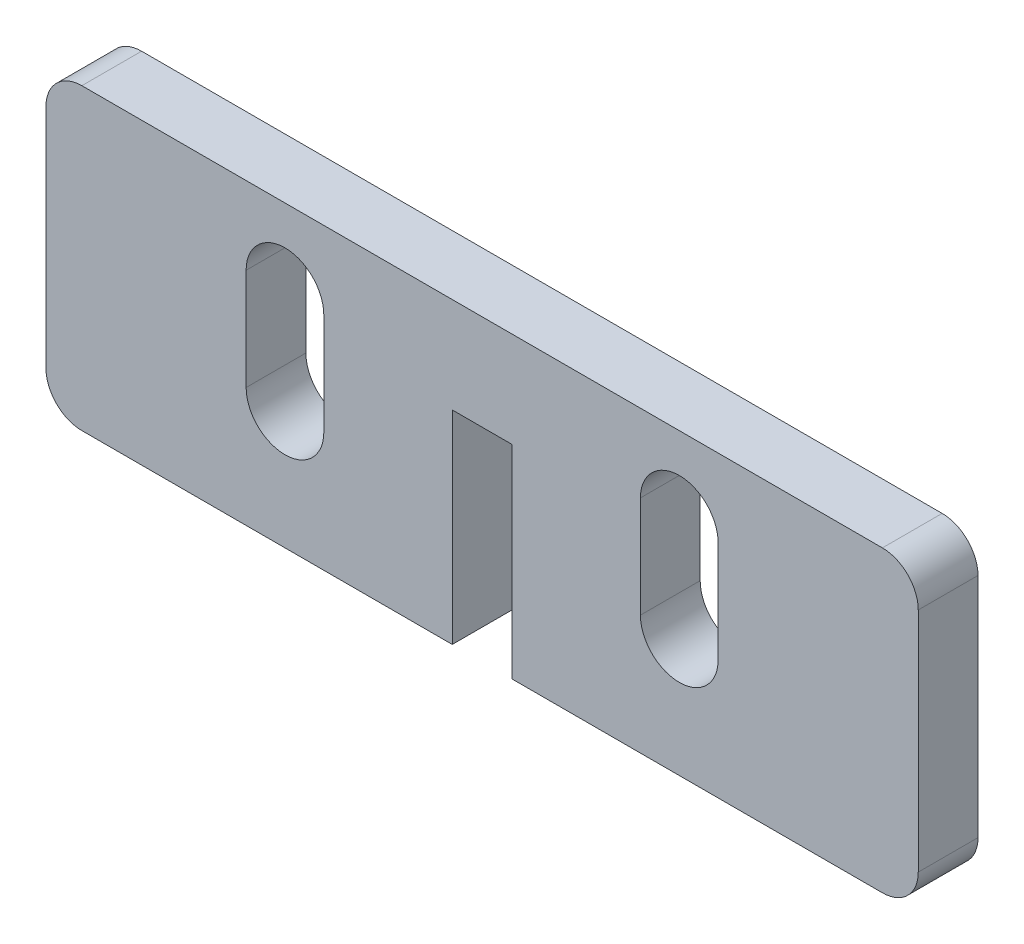
SolidWorks part; units mm, degrees
ref_plane "前视基准面" through (0, 0, 0) normal (0, 0, 1) x (1, 0, 0)
ref_plane "上视基准面" through (0, 0, 0) normal (0, 1, 0) x (1, 0, 0)
ref_plane "右视基准面" through (0, 0, 0) normal (1, 0, 0) x (0, 0, -1)
sketch "草图1" plane through (0, 0, 0) normal (0, 0, 1) x (1, 0, 0)
  line L0 (-16.5, -2.5) -> (-16.5, 6) construction
  line L1 (33.5, -12.5) -> (-33.5, -12.5) construction
  line L2 (36.5, -9.5) -> (36.5, 9.5)
  line L3 (33.5, 12.5) -> (-33.5, 12.5)
  line L4 (-36.5, -9.5) -> (-36.5, 9.5)
  line L5 (0, 12.5) -> (0, -12.5) construction
  line L6 (36.5, 0) -> (-36.5, 0) construction
  line L7 (2.5, 2.5) -> (-2.5, 2.5)
  line L8 (2.5, 2.5) -> (2.5, -12.5)
  line L9 (2.5, -12.5) -> (-2.5, -12.5) construction
  line L10 (-2.5, 2.5) -> (-2.5, -12.5)
  line L11 (0, -12.5) -> (0, 2.5) construction
  line L12 (2.5, -5) -> (-2.5, -5) construction
  line L13 (-19.75, -2.5) -> (-19.75, 6)
  line L14 (-13.25, -2.5) -> (-13.25, 6)
  line L15 (16.5, -2.5) -> (16.5, 6) construction
  line L16 (19.75, -2.5) -> (19.75, 6)
  line L17 (13.25, -2.5) -> (13.25, 6)
  line L18 (-33.5, -12.5) -> (-2.5, -12.5)
  line L19 (2.5, -12.5) -> (33.5, -12.5)
  arc A0 (-19.75, -2.5) -> (-13.25, -2.5) centre (-16.5, -2.5) ccw
  arc A1 (-13.25, 6) -> (-19.75, 6) centre (-16.5, 6) ccw
  arc A2 (19.75, -2.5) -> (13.25, -2.5) centre (16.5, -2.5) cw
  arc A3 (13.25, 6) -> (19.75, 6) centre (16.5, 6) cw
  arc A4 (33.5, -12.5) -> (36.5, -9.5) centre (33.5, -9.5) ccw
  arc A5 (-33.5, -12.5) -> (-36.5, -9.5) centre (-33.5, -9.5) cw
  arc A6 (36.5, 9.5) -> (33.5, 12.5) centre (33.5, 9.5) ccw
  arc A7 (-33.5, 12.5) -> (-36.5, 9.5) centre (-33.5, 9.5) ccw
  point P0 (0, 0)
  point P4 (0, -5)
  point P13 (-16.5, 1.75)
  point P21 (-16.5, 9.25)
  point P22 (-16.5, -5.75)
  point P25 (16.5, 1.75)
  point P32 (36.5, -12.5)
  point P37 (36.5, 12.5)
  point P40 (-36.5, 12.5)
  dimension "D9" = 3
  dimension "D1" = 73
  dimension "D2" = 25
  dimension "D3" = 5
  dimension "D4" = 15
  dimension "D5" = 3.25
  dimension "D6" = 10.75
  dimension "D7" = 6.5
  dimension "D8" = 15
extrude "凸台-拉伸1" add sketch "草图1" along normal blind 5
sketch "草图3" plane through (0, 0, 0) normal (0, 0, -1) x (-1, 0, 0)
  line L0 (-2.5, 2.5) -> (-2.5, 4.5)
  line L1 (-2.5, 4.5) -> (2.5, 4.5)
  line L2 (2.5, 4.5) -> (2.5, 2.5)
  line L3 (2.5, 2.5) -> (-2.5, 2.5)
  dimension "D1" = 2
extrude "切除-拉伸2" cut sketch "草图3" against normal blind 10
